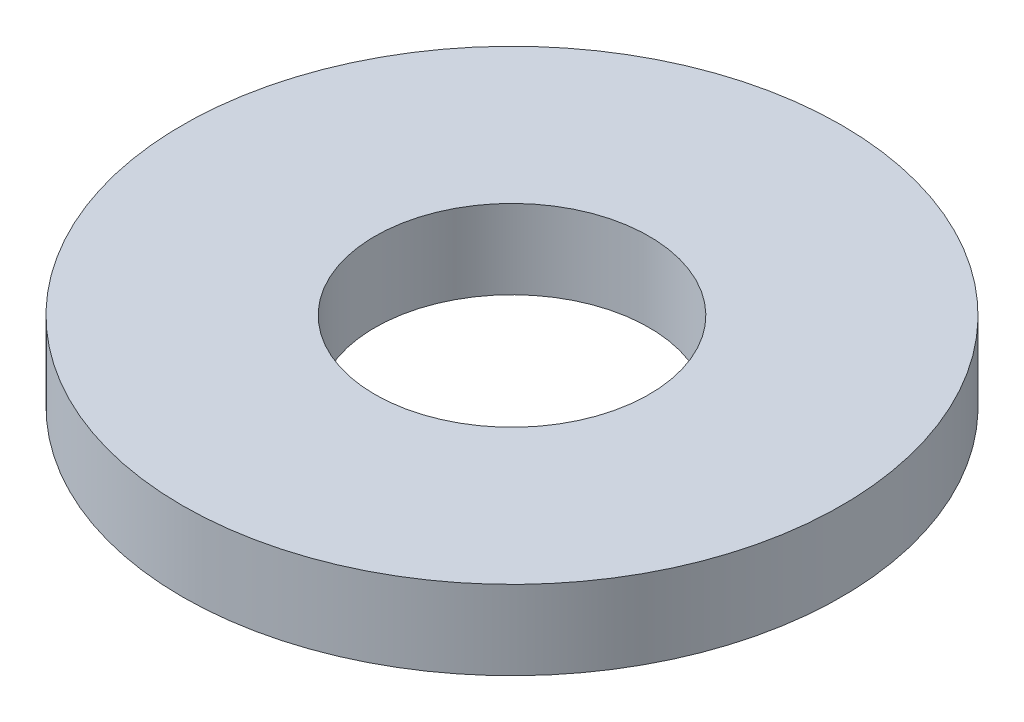
SolidWorks part; units mm, degrees
ref_plane "Front Plane" through (0, 0, 0) normal (0, 0, 1) x (1, 0, 0)
ref_plane "Top Plane" through (0, 0, 0) normal (0, 1, 0) x (1, 0, 0)
ref_plane "Right Plane" through (0, 0, 0) normal (1, 0, 0) x (0, 0, -1)
sketch "Sketch1" plane through (0, 0, 0) normal (0, 1, 0) x (1, 0, 0)
  circle A0 centre (0, 0) radius 4.7625
  dimension "OD" = 9.525
extrude "Boss-Extrude1" add sketch "Sketch1" along normal blind 1.143
sketch "Sketch5" plane through (0, 1.143, 0) normal (0, 1, 0) x (-1, 0, 0)
  circle A0 centre (0, 0) radius 1.9812
  dimension "ID" = 3.9624
extrude "Cut-Extrude1" cut sketch "Sketch5" against normal through all
